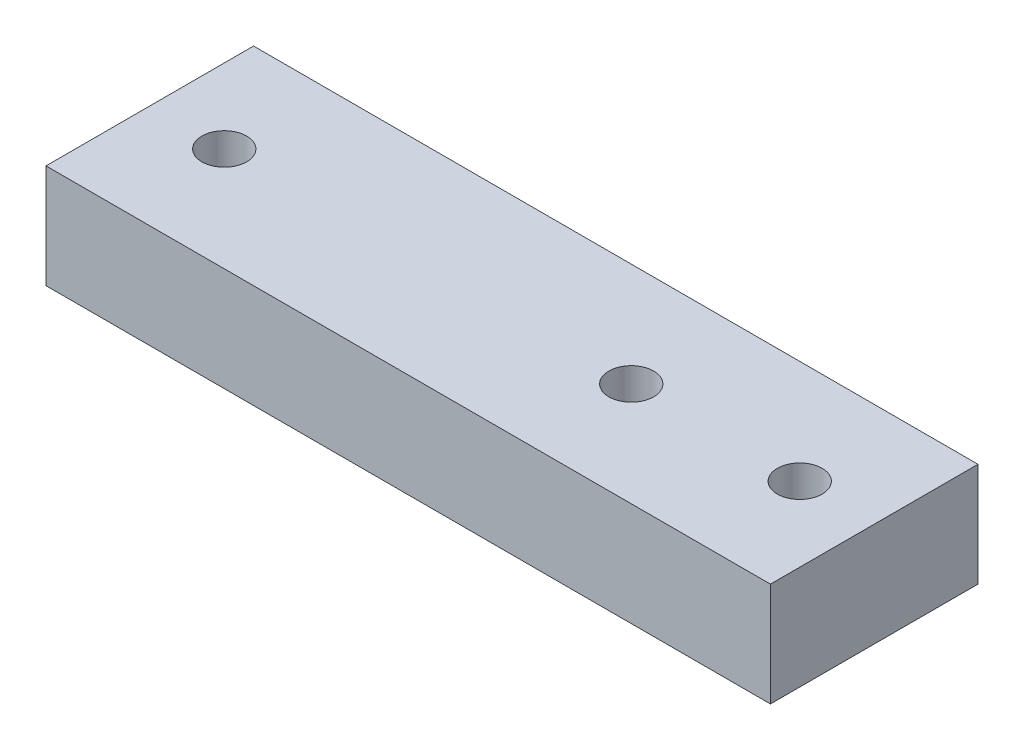
SolidWorks part; units mm, degrees
ref_plane "Plano frontal" through (0, 0, 0) normal (0, 0, 1) x (1, 0, 0)
ref_plane "Plano superior" through (0, 0, 0) normal (0, 1, 0) x (1, 0, 0)
ref_plane "Plano direito" through (0, 0, 0) normal (1, 0, 0) x (0, 0, -1)
sketch "Esboço1" plane through (0, 0, 0) normal (0, 1, 0) x (1, 0, 0)
  line L0 (0, 12.75) -> (-89, 12.75) construction
  line L1 (0, 0) -> (-89, 0)
  line L2 (0, 0) -> (0, 25.5)
  line L3 (0, 25.5) -> (-89, 25.5)
  line L4 (-89, 0) -> (-89, 25.5)
  line L5 (-44.5, 0) -> (-44.5, 25.5) construction
  circle A0 centre (-79.85, 12.75) radius 2.75
  circle A1 centre (-9.15, 12.75) radius 2.75
  circle A2 centre (-29.85, 12.75) radius 2.75
  dimension "D1" = 89
  dimension "D2" = 25.5
extrude "Ressalto-extrusão1" add sketch "Esboço1" along normal blind 12.75
